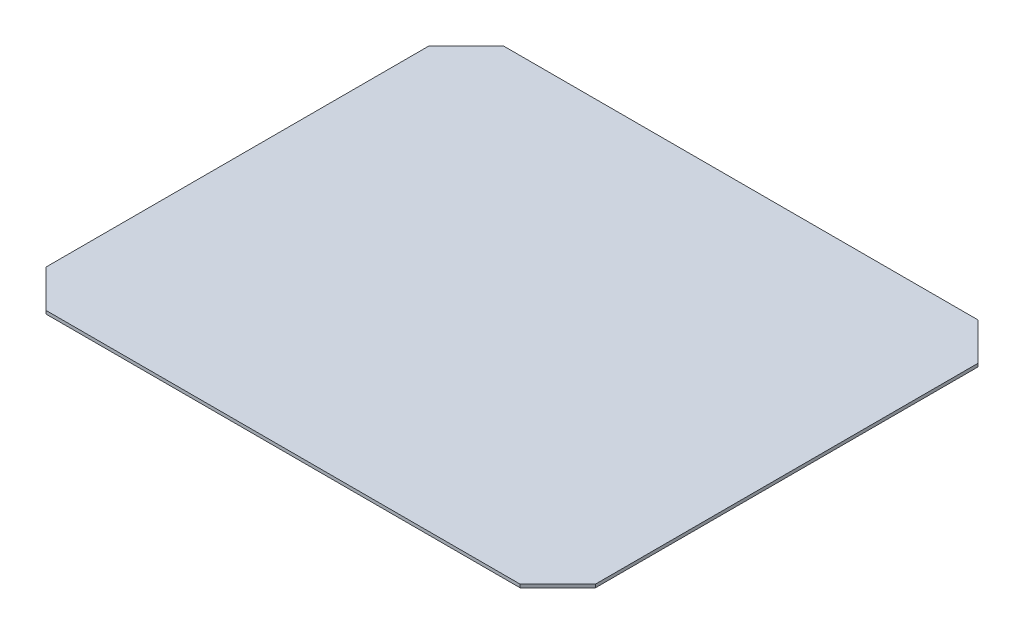
SolidWorks part; units mm, degrees
ref_plane "Front Plane" through (0, 0, 0) normal (0, 0, 1) x (1, 0, 0)
ref_plane "Top Plane" through (0, 0, 0) normal (0, 1, 0) x (1, 0, 0)
ref_plane "Right Plane" through (0, 0, 0) normal (1, 0, 0) x (0, 0, -1)
sketch "Sketch1" plane through (0, 0, 0) normal (0, 1, 0) x (1, 0, 0)
  line L1 (-280, 230) -> (260, 230)
  line L2 (-320, 210) -> (-320, -250)
  line L3 (-280, -270) -> (260, -270)
  line L4 (280, 210) -> (280, -250)
  line L25 (-280, -270) -> (-320, -270)
  line L26 (-320, -250) -> (-320, -270)
  line L29 (260, -270) -> (280, -270)
  line L30 (280, -250) -> (280, -270)
  line L31 (260, 230) -> (280, 230)
  line L32 (280, 210) -> (280, 230)
  line L35 (-280, 230) -> (-320, 230)
  line L36 (-320, 210) -> (-320, 230)
  point P0 (0, 0)
  dimension "D2" = 500
  dimension "D11" = 600
extrude "Boss-Extrude1" add sketch "Sketch1" along normal blind 3.5
sketch "Sketch2" plane through (0, 3.5, 0) normal (0, 1, 0) x (1, 0, 0)
  line L0 (-320, -229) -> (-320, -270)
  line L1 (-320, 230) -> (-320, -270) construction
  line L2 (-320, -270) -> (-279, -270)
  line L3 (-320, -270) -> (280, -270) construction
  line L4 (-279, -270) -> (-320, -229)
  line L5 (-320, -20) -> (280, -20) construction
  line L6 (280, -270) -> (280, 230) construction
  line L7 (-20, 230) -> (-20, -270) construction
  line L8 (280, 230) -> (-320, 230) construction
  line L9 (-320, 230) -> (-279, 230)
  line L10 (-320, 189) -> (-320, 230)
  line L11 (-279, 230) -> (-320, 189)
  line L12 (280, -270) -> (239, -270)
  line L13 (280, -229) -> (280, -270)
  line L14 (239, -270) -> (280, -229)
  line L15 (280, 189) -> (280, 230)
  line L16 (239, 230) -> (280, 189)
  line L17 (280, 230) -> (239, 230)
  dimension "D1" = 41
  dimension "D2" = 41
extrude "Cut-Extrude1" cut sketch "Sketch2" against normal through all
